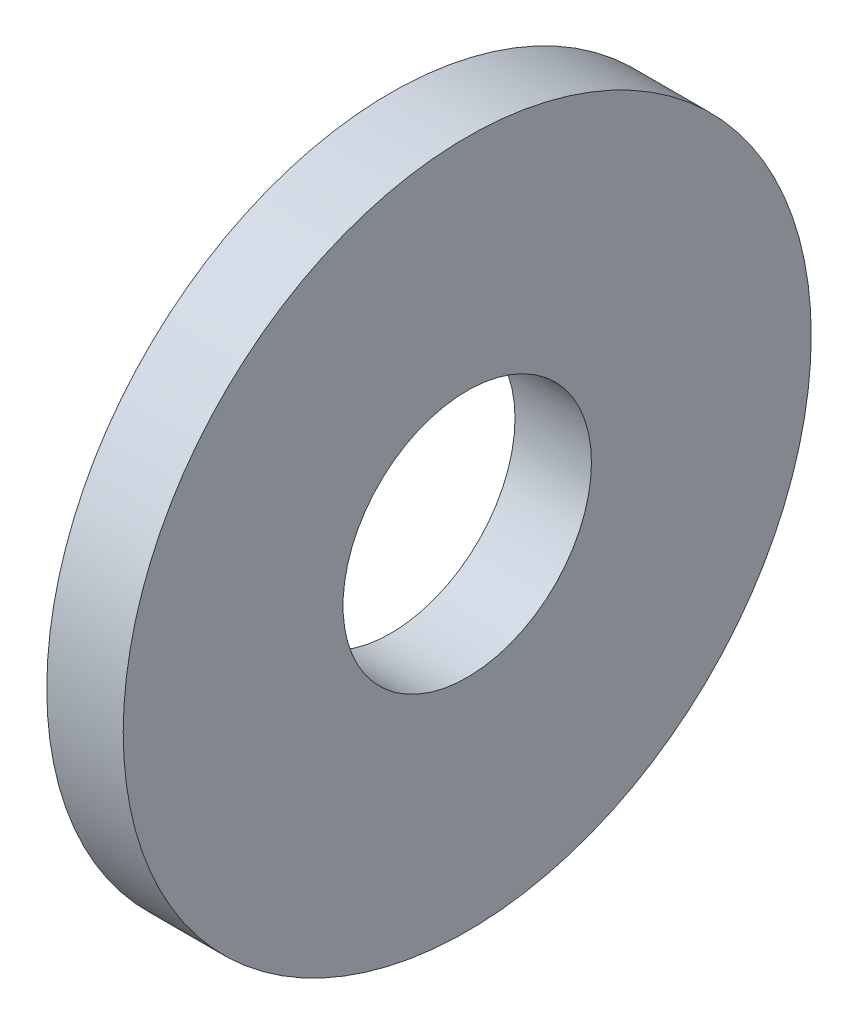
SolidWorks part; units mm, degrees
material "Pine"
ref_plane "Front Plane" through (0, 0, 0) normal (0, 0, 1) x (1, 0, 0)
ref_plane "Top Plane" through (0, 0, 0) normal (0, 1, 0) x (1, 0, 0)
ref_plane "Right Plane" through (0, 0, 0) normal (1, 0, 0) x (0, 0, -1)
sketch "Sketch1" plane through (0, 0, 0) normal (1, 0, 0) x (0, 0, -1)
  circle A0 centre (0, 0) radius 9
  dimension "D1" = 18
extrude "Boss-Extrude1" add sketch "Sketch1" along normal blind 2
sketch "Sketch2" plane through (2, 0, 0) normal (1, 0, 0) x (0, 0, -1)
  circle A2 centre (0, 0) radius 3.25
  dimension "D1" = 6.5
extrude "Cut-Extrude1" cut sketch "Sketch2" against normal through all
